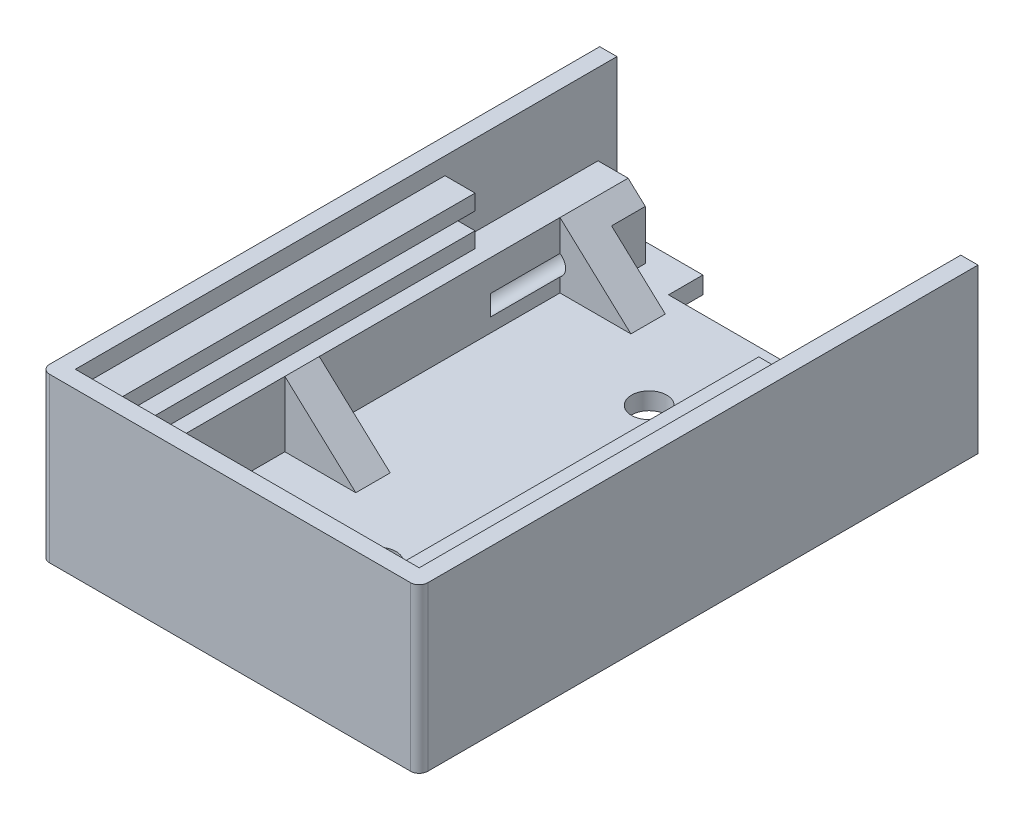
SolidWorks part; units mm, degrees
ref_plane "Plano frontal" through (0, 0, 0) normal (0, 0, 1) x (1, 0, 0)
ref_plane "Plano superior" through (0, 0, 0) normal (0, 1, 0) x (1, 0, 0)
ref_plane "Plano direito" through (0, 0, 0) normal (1, 0, 0) x (0, 0, -1)
sketch "Esboço1" plane through (0, 0, 0) normal (0, 1, 0) x (1, 0, 0)
  line L1 (-22, 32.5) -> (22, 32.5)
  line L2 (-22, 32.5) -> (-22, -32.5)
  line L3 (-22, -32.5) -> (22, -32.5)
  line L4 (22, 32.5) -> (22, -32.5)
  line L5 (-22, 32.5) -> (22, -32.5) construction
  line L6 (-22, -32.5) -> (22, 32.5) construction
  point P0 (0, 0)
  dimension "D1" = 65
  dimension "D2" = 44
extrude "Ressalto-extrusão1" add sketch "Esboço1" along normal blind 19
sketch "Esboço2" plane through (0, 0, -32.5) normal (0, 0, -1) x (-1, 0, 0)
  line L0 (0, 19) -> (0, 0) construction
  line L1 (-22, 19) -> (22, 19) construction
  line L2 (0, 0) -> (-22, 9.5) construction
  line L3 (-22, 19) -> (-22, 0) construction
  line L4 (-22, 9.5) -> (22, 9.5) construction
  line L5 (22, 19) -> (22, 0) construction
  line L7 (-20, 17) -> (20, 17)
  line L8 (-20, 17) -> (-20, 2)
  line L9 (-20, 2) -> (20, 2)
  line L10 (20, 17) -> (20, 2)
  line L11 (-20, 17) -> (20, 2) construction
  line L12 (-20, 2) -> (20, 17) construction
  point P5 (0, 9.5)
  dimension "D1" = 40
  dimension "D2" = 15
extrude "Corte-extrusão1" cut sketch "Esboço2" against normal blind 20
sketch "Esboço3" plane through (0, 0, -12.5) normal (0, 0, -1) x (-1, 0, 0)
  line L0 (0, 17) -> (0, 10.5) construction
  line L1 (20, 17) -> (-20, 17) construction
  line L3 (-20, 11.4) -> (20, 11.4)
  line L4 (-20, 11.4) -> (-20, 9.6)
  line L5 (-20, 9.6) -> (20, 9.6)
  line L6 (20, 11.4) -> (20, 9.6)
  line L7 (-20, 11.4) -> (20, 9.6) construction
  line L8 (-20, 9.6) -> (20, 11.4) construction
  dimension "D1" = 6.5
  dimension "D2" = 1.8
  dimension "D3" = 40
extrude "Corte-extrusão2" cut sketch "Esboço3" against normal blind 43
sketch "Esboço4" plane through (0, 0, -12.5) normal (0, 0, -1) x (-1, 0, 0)
  line L0 (0, 2) -> (0, 9.6) construction
  line L1 (-20, 2) -> (20, 2) construction
  line L2 (-20, 9.6) -> (20, 9.6) construction
  line L4 (-16.5, 9.6) -> (16.5, 9.6)
  line L5 (-16.5, 9.6) -> (-16.5, 2)
  line L6 (-16.5, 2) -> (16.5, 2)
  line L7 (16.5, 9.6) -> (16.5, 2)
  line L8 (-16.5, 9.6) -> (16.5, 2) construction
  line L9 (-16.5, 2) -> (16.5, 9.6) construction
  point P6 (0, 5.8)
  dimension "D1" = 7.6
  dimension "D2" = 33
extrude "Corte-extrusão3" cut sketch "Esboço4" against normal blind 43
sketch "Esboço5" plane through (0, 0, -12.5) normal (0, 0, -1) x (-1, 0, 0)
  line L4 (-16.5, 2) -> (-16.5, 9.6)
  line L5 (-16.5, 9.6) -> (-20, 9.6)
  line L6 (-20, 9.6) -> (-20, 2)
  line L7 (-20, 2) -> (-16.5, 2)
  line L8 (-16.5, 2) -> (-16.5, 9.6)
  line L9 (-16.5, 9.6) -> (-20, 9.6)
  line L10 (-20, 9.6) -> (-20, 2)
  line L11 (-20, 2) -> (-16.5, 2)
  line L12 (16.5, 9.6) -> (16.5, 2)
  line L13 (16.5, 2) -> (20, 2)
  line L14 (20, 2) -> (20, 9.6)
  line L15 (20, 9.6) -> (16.5, 9.6)
  line L16 (16.5, 9.6) -> (16.5, 2)
  line L17 (16.5, 2) -> (20, 2)
  line L18 (20, 2) -> (20, 9.6)
  line L19 (20, 9.6) -> (16.5, 9.6)
  dimension "D1" = 0
  dimension "D2" = 0
extrude "Ressalto-extrusão2" add sketch "Esboço5" along normal blind 20
sketch "Esboço6" plane through (0, 0, -12.5) normal (0, 0, -1) x (-1, 0, 0)
  line L0 (0, 17) -> (0, 11.4) construction
  line L1 (20, 17) -> (-20, 17) construction
  line L2 (20, 11.4) -> (-20, 11.4) construction
  line L3 (20, 11.4) -> (-20, 11.4) construction
  line L4 (-16.5, 17) -> (16.5, 17)
  line L5 (-16.5, 17) -> (-16.5, 11.4)
  line L6 (-16.5, 11.4) -> (16.5, 11.4)
  line L7 (16.5, 17) -> (16.5, 11.4)
  line L8 (-16.5, 17) -> (16.5, 11.4) construction
  line L9 (-16.5, 11.4) -> (16.5, 17) construction
  point P6 (0, 14.2)
extrude "Corte-extrusão4" cut sketch "Esboço6" against normal blind 43
sketch "Esboço7" plane through (0, 0, -32.5) normal (0, 0, -1) x (-1, 0, 0)
  line L0 (-18.25, 11.4) -> (-18.25, 17) construction
  line L1 (-16.5, 11.4) -> (-20, 11.4) construction
  line L2 (-16.5, 17) -> (-20, 17) construction
  line L3 (-16.5, 17) -> (-16.5, 11.4) construction
  line L4 (-20, 15.2) -> (-16.5, 15.2)
  line L5 (-20, 15.2) -> (-20, 13.2)
  line L6 (-20, 13.2) -> (-16.5, 13.2)
  line L7 (-16.5, 15.2) -> (-16.5, 13.2)
  line L8 (-20, 15.2) -> (-16.5, 13.2) construction
  line L9 (-20, 13.2) -> (-16.5, 15.2) construction
  line L10 (18.25, 11.4) -> (18.25, 17) construction
  line L11 (20, 11.4) -> (16.5, 11.4) construction
  line L12 (20, 17) -> (16.5, 17) construction
  line L13 (20, 11.4) -> (20, 17) construction
  line L14 (16.5, 15.2) -> (20, 15.2)
  line L15 (16.5, 15.2) -> (16.5, 13.2)
  line L16 (16.5, 13.2) -> (20, 13.2)
  line L17 (20, 15.2) -> (20, 13.2)
  line L18 (16.5, 15.2) -> (20, 13.2) construction
  line L19 (16.5, 13.2) -> (20, 15.2) construction
  line L20 (-22, 19) -> (22, 19) construction
  line L21 (-20, 17) -> (20, 17)
  line L22 (-20, 17) -> (-20, 19)
  line L23 (-20, 19) -> (20, 19)
  line L24 (20, 17) -> (20, 19)
  point P6 (-18.25, 14.2)
  point P19 (18.25, 14.2)
  dimension "D1" = 2
  dimension "D2" = 2
extrude "Corte-extrusão5" cut sketch "Esboço7" against normal blind 63
sketch "Esboço8" plane through (0, 2, 0) normal (0, 1, 0) x (1, 0, 0)
  line L0 (0, -30.5) -> (0, 0) construction
  line L1 (16.5, -30.5) -> (-16.5, -30.5) construction
  line L2 (0, 0) -> (0, 32.5) construction
  line L3 (16.5, 32.5) -> (-16.5, 32.5) construction
  circle A0 centre (0, 16.25) radius 2.05
  circle A1 centre (0, -15.25) radius 2.05
  dimension "D1" = 4.1
  dimension "D2" = 4.1
extrude "Corte-extrusão6" cut sketch "Esboço8" against normal through all
sketch "Esboço9" plane through (0, 0, -32.5) normal (0, 0, -1) x (-1, 0, 0)
  line L1 (16.5, 9.6) -> (20, 9.6)
  line L2 (16.5, 9.6) -> (16.5, 1.9987)
  line L3 (16.5, 1.9987) -> (20, 1.9987)
  line L4 (20, 9.6) -> (20, 1.9987)
  line L5 (-20, 1.9987) -> (-16.5, 1.9987)
  line L6 (-20, 1.9987) -> (-20, 9.6)
  line L7 (-20, 9.6) -> (-16.5, 9.6)
  line L8 (-16.5, 1.9987) -> (-16.5, 9.6)
extrude "Corte-extrusão7" cut sketch "Esboço9" against normal blind 4
sketch "Esboço10" plane through (0, 0, -28.5) normal (0, 0, -1) x (-1, 0, 0)
  line L0 (-20, 9.6) -> (-20, 1.9987) construction
  line L1 (-16.5, 9.6) -> (-20, 9.6)
  line L2 (-16.5, 9.6) -> (-16.5, 7.6)
  line L3 (-16.5, 7.6) -> (-20, 7.6)
  line L4 (-20, 9.6) -> (-20, 7.6)
  dimension "D2" = 2
extrude "Corte-extrusão9" cut sketch "Esboço10" against normal blind 16
sketch "Esboço12" plane through (0, 2, 0) normal (0, 1, 0) x (1, 0, 0)
  line L0 (0, 32.5) -> (0, -30.5) construction
  line L1 (16.5, 32.5) -> (-16.5, 32.5) construction
  line L2 (-20, -30.5) -> (20, -30.5) construction
  line L3 (0, 0) -> (16.5, 0) construction
  line L4 (16.5, -30.5) -> (16.5, 28.5) construction
  line L5 (8.25, 0) -> (8.25, -30.5) construction
  line L6 (16.5, -30.5) -> (-16.5, -30.5) construction
  line L7 (8.25, 0) -> (8.25, 32.5) construction
  line L8 (8.25, 16.25) -> (16.5, 16.25) construction
  line L9 (8.25, -15.25) -> (16.5, -15.25) construction
  line L10 (16.5, -15.25) -> (12.375, -15.25) construction
  line L11 (12.375, -15.25) -> (12.375, -30.5) construction
  line L12 (12.375, -15.25) -> (12.375, 0) construction
  line L13 (12.375, 0) -> (12.375, 16.25) construction
  line L14 (12.375, 16.25) -> (12.375, 32.5) construction
  line L15 (12.375, 24.375) -> (-16.5, 24.375) construction
  line L16 (-16.5, -30.5) -> (-16.5, 28.5) construction
  line L17 (-16.5, 24.375) -> (12.375, 8.125) construction
  line L18 (12.375, 8.125) -> (-16.5, 8.125) construction
  line L19 (-16.5, -30.5) -> (-16.5, 28.5) construction
  line L20 (-16.5, 8.125) -> (12.375, -7.625) construction
  line L21 (12.375, -7.625) -> (-16.5, -7.625) construction
  line L22 (-16.5, -7.625) -> (12.375, -22.875) construction
  line L23 (12.375, -22.875) -> (-16.5, -22.875) construction
  line L24 (0, 32.5) -> (-16.5, 32.5) construction
  line L25 (-8.25, 32.5) -> (-8.25, -30.5) construction
  line L26 (0, 32.5) -> (16.5, 32.5) construction
  line L27 (-16.5, 32.5) -> (-8.25, 32.5) construction
  line L28 (-8.25, 32.5) -> (-12.375, 32.5) construction
  line L29 (-12.375, 32.5) -> (-12.375, -30.5) construction
  line L30 (-12.375, -30.5) -> (-12.375, -22.875) construction
  line L31 (-12.375, -22.875) -> (-12.375, -26.6875) construction
  line L32 (-12.375, -26.6875) -> (16.5, -26.6875) construction
  line L33 (16.5, -30.5) -> (16.5, 12.5) construction
  line L34 (16.5, -26.6875) -> (8.25, -26.6875) construction
  line L35 (8.25, -26.6875) -> (12.375, -26.6875) construction
  line L37 (16.5, 26.375) -> (8.25, 26.375)
  line L38 (16.5, 26.375) -> (16.5, 22.375)
  line L39 (16.5, 22.375) -> (8.25, 22.375)
  line L40 (8.25, 26.375) -> (8.25, 22.375)
  line L41 (16.5, 26.375) -> (8.25, 22.375) construction
  line L42 (16.5, 22.375) -> (8.25, 26.375) construction
  line L47 (16.5, 10.125) -> (8.25, 6.125) construction
  line L48 (16.5, 6.125) -> (8.25, 10.125) construction
  line L49 (16.5, -5.625) -> (8.25, -5.625)
  line L50 (16.5, -5.625) -> (16.5, -9.625)
  line L51 (16.5, -9.625) -> (8.25, -9.625)
  line L52 (8.25, -5.625) -> (8.25, -9.625)
  line L53 (16.5, -5.625) -> (8.25, -9.625) construction
  line L54 (16.5, -9.625) -> (8.25, -5.625) construction
  line L55 (10.25, -22.875) -> (6.25, -22.875)
  line L56 (10.25, -22.875) -> (10.25, -30.5)
  line L57 (10.25, -30.5) -> (6.25, -30.5)
  line L58 (6.25, -22.875) -> (6.25, -30.5)
  line L59 (10.25, -22.875) -> (6.25, -30.5) construction
  line L60 (10.25, -30.5) -> (6.25, -22.875) construction
  line L65 (2, -22.875) -> (-2, -30.5) construction
  line L66 (2, -30.5) -> (-2, -22.875) construction
  line L67 (-6.25, -22.875) -> (-10.25, -22.875)
  line L68 (-6.25, -22.875) -> (-6.25, -30.5)
  line L69 (-6.25, -30.5) -> (-10.25, -30.5)
  line L70 (-10.25, -22.875) -> (-10.25, -30.5)
  line L71 (-6.25, -22.875) -> (-10.25, -30.5) construction
  line L72 (-6.25, -30.5) -> (-10.25, -22.875) construction
  line L73 (-16.5, -5.625) -> (-8.25, -5.625)
  line L74 (-16.5, -5.625) -> (-16.5, -9.625)
  line L75 (-16.5, -9.625) -> (-8.25, -9.625)
  line L76 (-8.25, -5.625) -> (-8.25, -9.625)
  line L77 (-16.5, -5.625) -> (-8.25, -9.625) construction
  line L78 (-16.5, -9.625) -> (-8.25, -5.625) construction
  line L83 (-16.5, 10.125) -> (-8.25, 6.125) construction
  line L84 (-16.5, 6.125) -> (-8.25, 10.125) construction
  line L85 (-16.5, 26.375) -> (-8.25, 26.375)
  line L86 (-16.5, 26.375) -> (-16.5, 22.375)
  line L87 (-16.5, 22.375) -> (-8.25, 22.375)
  line L88 (-8.25, 26.375) -> (-8.25, 22.375)
  line L89 (-16.5, 26.375) -> (-8.25, 22.375) construction
  line L90 (-16.5, 22.375) -> (-8.25, 26.375) construction
  point P68 (0, -26.6875)
  point P73 (-8.25, -26.6875)
  point P78 (-12.375, -7.625)
  point P83 (-12.375, 8.125)
  point P88 (-12.375, 24.375)
  dimension "D1" = 4
  dimension "D2" = 4
  dimension "D3" = 4
  dimension "D4" = 4
  dimension "D5" = 4
  dimension "D6" = 4
  dimension "D7" = 4
  dimension "D8" = 4
  dimension "D9" = 4
extrude "Ressalto-extrusão3" add sketch "Esboço12" along normal blind 8
sketch "Esboço13" plane through (0, 0, -26.375) normal (0, 0, -1) x (-1, 0, 0)
  line L0 (8.25, 2) -> (16.5, 9.6)
  line L1 (16.5, 9.6) -> (16.5, 10)
  line L2 (8.25, 10) -> (16.5, 10) construction
  line L3 (8.25, 10) -> (8.25, 2)
  line L4 (10.25, 10) -> (6.25, 10) construction
  line L5 (-8.25, 2) -> (-16.5, 9.6)
  line L6 (-16.5, 9.6) -> (-16.5, 10)
  line L7 (-16.5, 10) -> (-8.25, 10)
  line L8 (-10.25, 10) -> (-6.25, 10) construction
  line L9 (-8.25, 10) -> (-8.25, 2)
  line M3 (16.5, 9.6) -> (16.5, 10)
  line M4 (16.5, 10) -> (8.25, 10)
  line M5 (8.25, 10) -> (8.25, 2)
extrude "Corte-extrusão10" cut sketch "Esboço13" against normal blind 40 contours L9 L7 L6 L5 | L0 M5 M3 M4
sketch "Esboço14" plane through (-10.25, 0, 0) normal (-1, 0, 0) x (0, 0, 1)
  line L0 (22.875, 2) -> (30.5, 9.625)
  line L1 (30.5, 10) -> (30.5, 2) construction
  line L2 (30.5, 9.625) -> (30.5, 10)
  line L3 (30.5, 11.4) -> (30.5, 9.6) construction
  line L4 (22.875, 10) -> (30.5, 10) construction
  line L5 (30.5, 10) -> (22.875, 10)
  line L6 (22.875, 2) -> (22.875, 10)
extrude "Corte-extrusão11" cut sketch "Esboço14" against normal blind 24
sketch "Esboço17" plane through (0, 0, -28.5) normal (0, 0, -1) x (-1, 0, 0)
  line L5 (-16.5, 2) -> (-16.5, 7.6)
  line L6 (-16.5, 7.6) -> (-20, 7.6)
  line L7 (-20, 7.6) -> (-20, 1.9987)
  line L8 (-20, 1.9987) -> (-16.5, 1.9987)
  line L9 (-16.5, 1.9987) -> (-16.5, 2)
  line L10 (-16.5, 2) -> (-16.5, 7.6)
  line L11 (-16.5, 7.6) -> (-20, 7.6)
  line L12 (-20, 7.6) -> (-20, 1.9987)
  line L13 (-20, 1.9987) -> (-16.5, 1.9987)
  line L14 (-16.5, 1.9987) -> (-16.5, 2)
  line L15 (16.5, 9.6) -> (16.5, 2)
  line L16 (16.5, 2) -> (16.5, 1.9987)
  line L17 (16.5, 1.9987) -> (20, 1.9987)
  line L18 (20, 1.9987) -> (20, 9.6)
  line L19 (20, 9.6) -> (16.5, 9.6)
  line L20 (16.5, 9.6) -> (16.5, 2)
  line L21 (16.5, 2) -> (16.5, 1.9987)
  line L22 (16.5, 1.9987) -> (20, 1.9987)
  line L23 (20, 1.9987) -> (20, 9.6)
  line L24 (20, 9.6) -> (16.5, 9.6)
  dimension "D1" = 0
  dimension "D2" = 0
extrude "Ressalto-extrusão4" add sketch "Esboço17" along normal blind 1.8
sketch "Esboço18" plane through (16.5, 0, 0) normal (-1, 0, 0) x (0, 0, 1)
  line L4 (-26.375, 2) -> (-26.375, 7.6)
  line L5 (-26.375, 7.6) -> (-30.3, 7.6)
  line L6 (-30.3, 7.6) -> (-30.3, 2)
  line L7 (-30.3, 2) -> (-26.375, 2)
  line L8 (-26.375, 2) -> (-26.375, 7.6)
  line L9 (-26.375, 7.6) -> (-30.3, 7.6)
  line L10 (-30.3, 7.6) -> (-30.3, 2)
  line L11 (-30.3, 2) -> (-26.375, 2)
  dimension "D1" = 0
extrude "Ressalto-extrusão5" add sketch "Esboço18" along normal blind 2
sketch "Esboço19" plane through (0, 0, -26.375) normal (0, 0, -1) x (-1, 0, 0)
  line L0 (-16.5, 9.6) -> (-16.5, 7.6)
  line L1 (-16.5, 7.6) -> (-14.2852, 7.5597)
  line L2 (-8.25, 2) -> (-16.5, 9.6) construction
  line L3 (-14.2852, 7.5597) -> (-16.5, 9.6)
extrude "Corte-extrusão12" cut sketch "Esboço19" against normal blind 10
sketch "Esboço20" plane through (0, 0, -30.3) normal (0, 0, -1) x (-1, 0, 0)
  line L0 (-14.5, 7.6) -> (-20, 1.9987) construction
  line L1 (-20, 1.9987) -> (-20, 7.6) construction
  line L2 (-20, 7.6) -> (-14.5, 2) construction
  circle A0 centre (-17.25, 4.7993) radius 1.4
  dimension "D1" = 2.8
extrude "Corte-extrusão13" cut sketch "Esboço20" against normal blind 16
sketch "Esboço21" plane through (-16.5, 0, 0) normal (1, 0, 0) x (0, 0, -1)
  line L4 (26.375, 9.6) -> (26.375, 2)
  line L5 (26.375, 2) -> (30.3, 2)
  line L6 (30.3, 2) -> (30.3, 9.6)
  line L7 (30.3, 9.6) -> (26.375, 9.6)
  line L8 (26.375, 9.6) -> (26.375, 2)
  line L9 (26.375, 2) -> (30.3, 2)
  line L10 (30.3, 2) -> (30.3, 9.6)
  line L11 (30.3, 9.6) -> (26.375, 9.6)
  dimension "D1" = 0
extrude "Ressalto-extrusão6" add sketch "Esboço21" along normal blind 2
sketch "Esboço23" plane through (0, 0, -30.3) normal (0, 0, -1) x (-1, 0, 0)
  line L0 (13.6246, 6.9511) -> (17.1021, 10.1547)
  line L1 (8.25, 2) -> (14.5, 7.7576) construction
  line L2 (17.1021, 10.1547) -> (13.6246, 10.1547)
  line L3 (13.6246, 10.1547) -> (13.6246, 6.9511)
extrude "Corte-extrusão14" cut sketch "Esboço23" against normal blind 5
sketch "Esboço24" plane through (0, 0, -30.3) normal (0, 0, -1) x (-1, 0, 0)
  line L0 (-14.5, 7.6) -> (20, 7.6) construction
  line L1 (20, 1.9987) -> (20, 19) construction
  line L2 (20, 7.6) -> (14.5, 2) construction
  line L3 (-16.5, 2) -> (16.5, 2) construction
  line L4 (8.25, 2) -> (14.5, 2) construction
  line L5 (14.5, 2) -> (20, 1.9987) construction
  line L6 (20, 1.9987) -> (14.5, 7.7576) construction
  line L7 (-17.25, 4.7993) -> (17.25, 4.8) construction
  circle A0 centre (17.25, 4.8) radius 1.4
  dimension "D1" = 2.8
extrude "Corte-extrusão15" cut sketch "Esboço24" against normal blind 16
sketch "Esboço26" plane through (0, 0, -32.5) normal (0, 0, -1) x (-1, 0, 0)
  line L0 (0, 2) -> (0, 0) construction
  line L1 (-6.25, 2) -> (6.25, 2) construction
  line L3 (-22, 0) -> (22, 0) construction
  line L4 (-10, 2) -> (10, 2)
  line L5 (-10, 2) -> (-10, 0)
  line L7 (-10, 0) -> (10, 0)
  line L8 (10, 2) -> (10, 0)
  line L9 (-10, 2) -> (10, 0) construction
  line L10 (-10, 0) -> (10, 2) construction
  point P6 (0, 1)
  dimension "D1" = 20
extrude "Corte-extrusão16" cut sketch "Esboço26" against normal blind 4
fillet "Filete1" radius 1 2 edges at (-22, 9.5, 32.5) (22, 9.5, 32.5)
